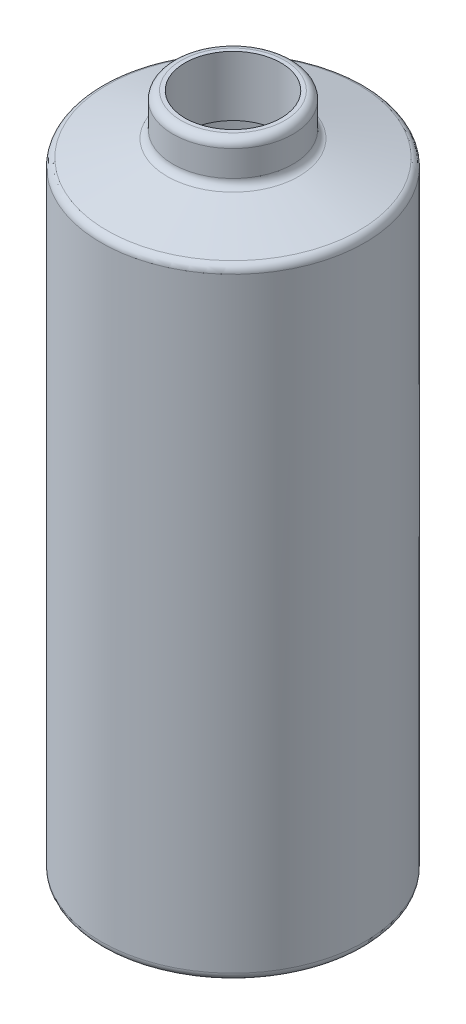
SolidWorks part; units mm, degrees
ref_plane "Front" through (0, 0, 0) normal (0, 0, 1) x (1, 0, 0)
ref_plane "Top" through (0, 0, 0) normal (0, 1, 0) x (1, 0, 0)
ref_plane "Right" through (0, 0, 0) normal (1, 0, 0) x (0, 0, -1)
sketch "Sketch1" plane through (0, 0, 0) normal (0, 1, 0) x (1, 0, 0)
  circle A0 centre (0, 0) radius 41.91
  dimension "D1" = 83.82
extrude "Boss-Extrude1" add sketch "Sketch1" along normal blind 196.85
ref_plane "Plane2" through (0, 203.2, 0) normal (0, 1, 0) x (1, 0, 0)
sketch "Sketch6" plane through (0, 203.2, 0) normal (0, 1, 0) x (1, 0, 0)
  circle A0 centre (0, 0) radius 19.05
  dimension "D1" = 38.1
extrude "Boss-Extrude4" add sketch "Sketch6" along normal blind 12.7 separate body
shell "Shell7" thickness 3.81
loft "Loft3" add section edge at (0, 196.85, 41.91) section edge at (0, 203.2, 19.05)
sketch "Sketch13" plane through (0, 215.9, 0) normal (0, 1, 0) x (1, 0, 0)
  circle A0 centre (0, 0) radius 15.24
  dimension "D1" = 30.48
extrude "Cut-Extrude2" cut sketch "Sketch13" against normal up to next
fillet "Fillet12" radius 2.54 4 edges at (0, 0, 41.91) (0, 196.85, 41.91) (0, 203.2, 19.05) (0, 215.9, 19.05)
